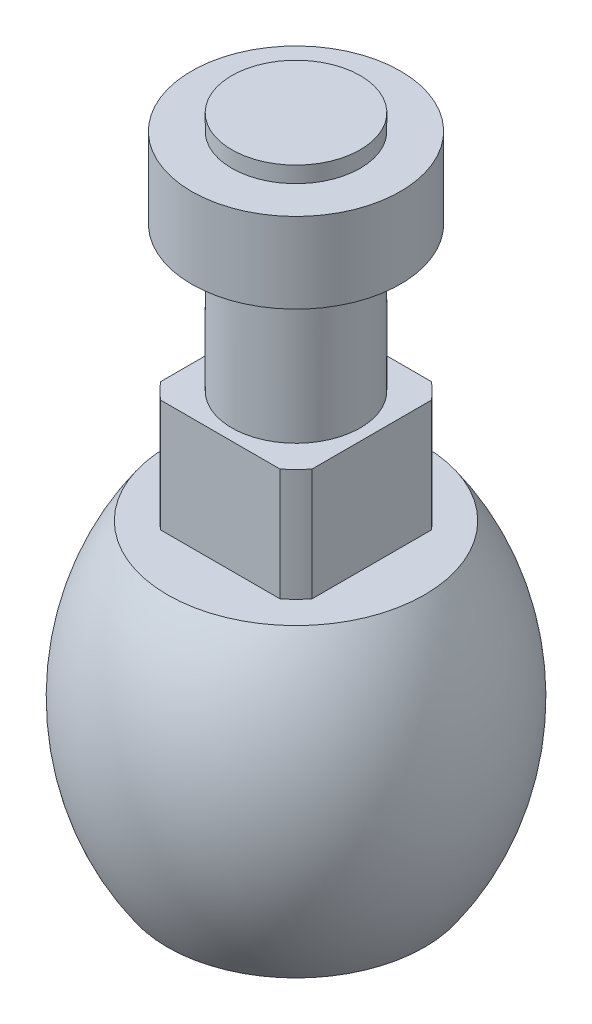
SolidWorks part; units mm, degrees
ref_plane "Front Plane" through (0, 0, 0) normal (0, 0, 1) x (1, 0, 0)
ref_plane "Top Plane" through (0, 0, 0) normal (0, 1, 0) x (1, 0, 0)
ref_plane "Right Plane" through (0, 0, 0) normal (1, 0, 0) x (0, 0, -1)
sketch "Sketch1" plane through (0, 0, 0) normal (0, 0, 1) x (1, 0, 0)
  line L0 (-8, 0) -> (0, 0)
  line L1 (0, 0) -> (0, 41)
  line L2 (0, 41) -> (-4, 41)
  line L3 (-4, 41) -> (-4, 26)
  line L8 (-4, 26) -> (-6, 26)
  line L9 (-6, 26) -> (-6, 19)
  line L10 (-6, 19) -> (-8, 19)
  arc A0 (-8, 19) -> (-8, 0) centre (5.5417, 9.5) ccw
  point P5 (0, 0)
  point P8 (-11, 9.5)
  dimension "D1" = 26
  dimension "D2" = 15
  dimension "D3" = 4
  dimension "D6" = 6
  dimension "D7" = 2
  dimension "D8" = 11
  dimension "D9" = 19
revolve "Revolve1" add sketch "Sketch1" angle 360 about L1
sketch "Sketch2" plane through (0, 26, 0) normal (0, 1, 0) x (1, 0, 0)
  line L0 (-3.7131, 4.7131) -> (3.7131, 4.7131)
  line L2 (4.7131, 3.7131) -> (4.7131, -3.7131)
  line L4 (3.7131, -4.7131) -> (-3.7131, -4.7131)
  line L6 (-4.7131, -3.7131) -> (-4.7131, 3.7131)
  arc A0 (-4.7131, 3.7131) -> (-4.7131, -3.7131) centre (0, 0) ccw
  arc A2 (3.7131, 4.7131) -> (-3.7131, 4.7131) centre (0, 0) ccw
  arc A3 (4.7131, -3.7131) -> (4.7131, 3.7131) centre (0, 0) ccw
  arc A4 (-3.7131, -4.7131) -> (3.7131, -4.7131) centre (0, 0) ccw
  dimension "D3" = 12
  dimension "D1" = 1
  dimension "D2" = 1
extrude "Cut-Extrude1" cut sketch "Sketch2" against normal up to surface (7 mm away) up to face at (0, 19, -8)
sketch "Sketch3" plane through (0, 0, 0) normal (0, -1, 0) x (1, 0, 0)
  circle A0 centre (0, 0) radius 5
  dimension "D1" = 10
extrude "Boss-Extrude1" add sketch "Sketch3" along normal blind 1
ref_plane "Plane1" through (0, 40, 0) normal (0, 1, 0) x (1, 0, 0)
sketch "Sketch4" plane through (0, 40, 0) normal (0, 1, 0) x (1, 0, 0)
  circle A0 centre (0, 0) radius 6.5
  dimension "D1" = 13
extrude "Boss-Extrude2" add sketch "Sketch4" against normal blind 5
